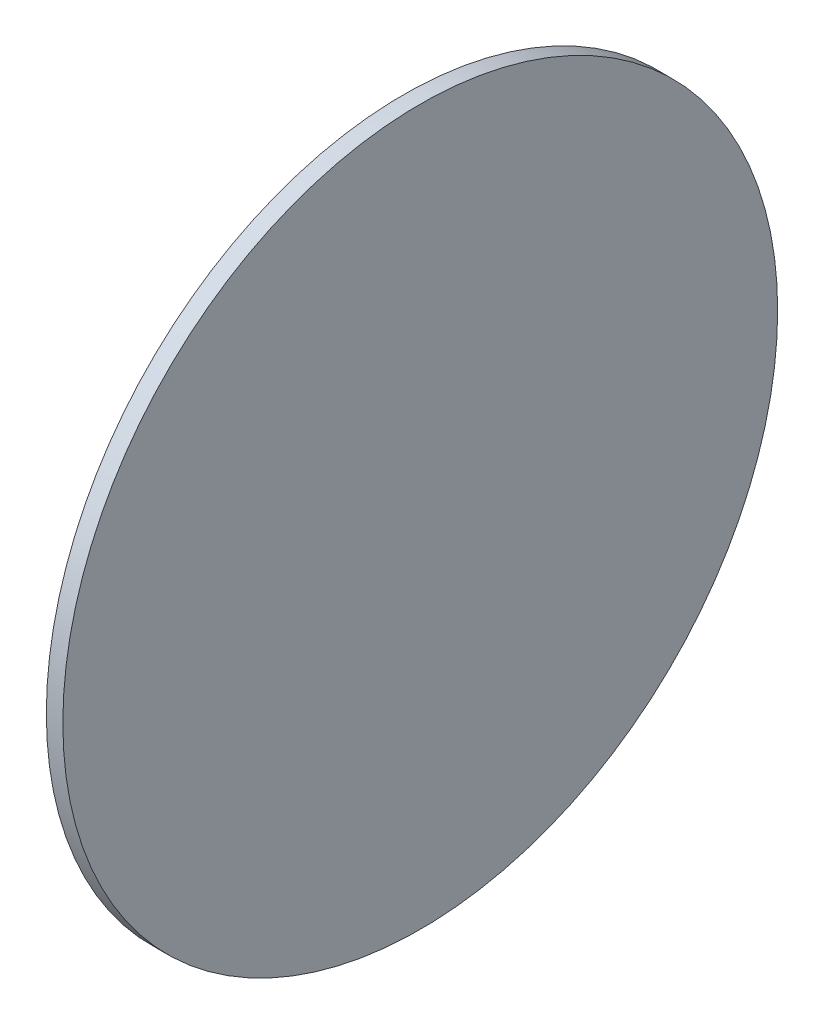
SolidWorks part; units mm, degrees
ref_plane "Front Plane" through (0, 0, 0) normal (0, 0, 1) x (1, 0, 0)
ref_plane "Top Plane" through (0, 0, 0) normal (0, 1, 0) x (1, 0, 0)
ref_plane "Right Plane" through (0, 0, 0) normal (1, 0, 0) x (0, 0, -1)
sketch "Sketch1" plane through (0, 0, 0) normal (-1, 0, 0) x (0, 0, 1)
  circle A0 centre (0, 0) radius 65
  point P3 (0, 0)
  point P4 (8.6133, 9.1768)
  point P5 (0, 0)
  point P6 (0, 0)
  dimension "D1" = 130
extrude "Boss-Extrude1" add sketch "Sketch1" against normal blind 3
